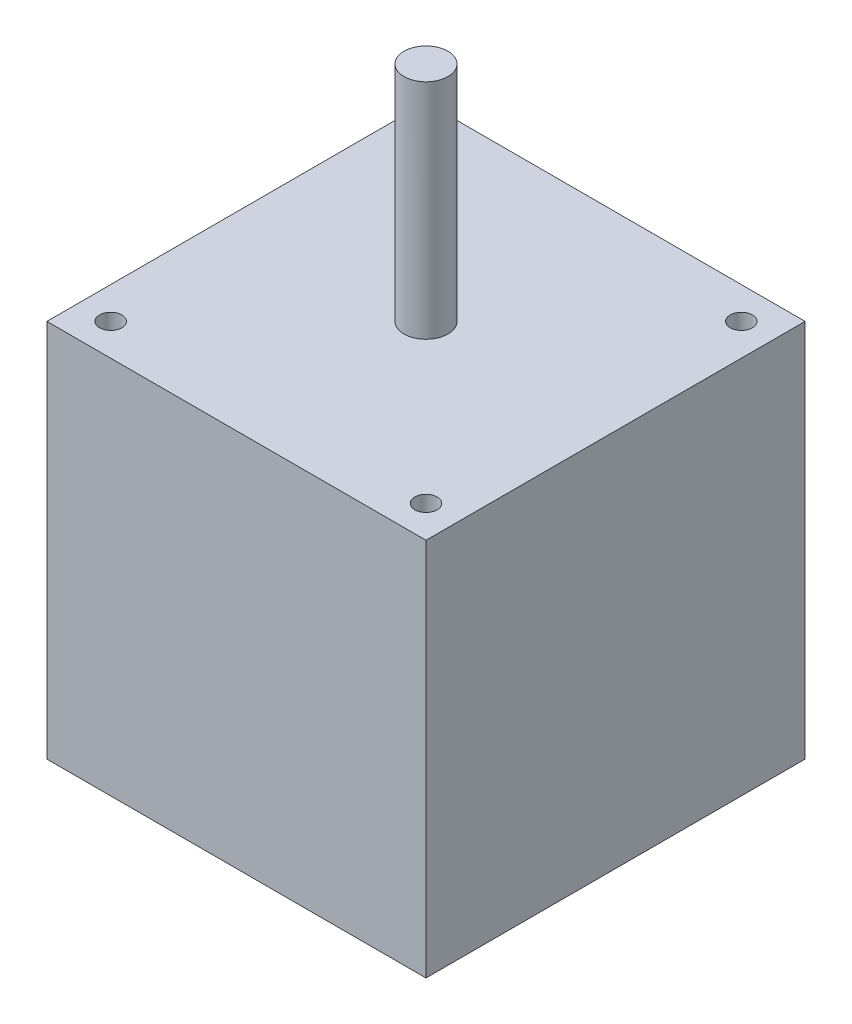
SolidWorks part; units mm, degrees
ref_plane "Front Plane" through (0, 0, 0) normal (0, 0, 1) x (1, 0, 0)
ref_plane "Top Plane" through (0, 0, 0) normal (0, 1, 0) x (1, 0, 0)
ref_plane "Right Plane" through (0, 0, 0) normal (1, 0, 0) x (0, 0, -1)
sketch "Sketch1" plane through (0, 0, 0) normal (0, 1, 0) x (1, 0, 0)
  line L1 (-21.59, -21.59) -> (21.59, -21.59)
  line L2 (-21.59, -21.59) -> (-21.59, 21.59)
  line L3 (-21.59, 21.59) -> (21.59, 21.59)
  line L4 (21.59, -21.59) -> (21.59, 21.59)
  line L5 (-21.59, -21.59) -> (21.59, 21.59) construction
  line L6 (-21.59, 21.59) -> (21.59, -21.59) construction
  point P0 (0, 0)
  dimension "D1" = 43.18
extrude "Boss-Extrude1" add sketch "Sketch1" along normal blind 43.18
sketch "Sketch2" plane through (0, 43.18, 0) normal (0, 1, 0) x (1, 0, 0)
  circle A0 centre (0, 0) radius 2.5
  dimension "D1" = 5
extrude "Boss-Extrude2" add sketch "Sketch2" along normal blind 25.4
sketch "Sketch3" plane through (0, 43.18, 0) normal (0, 1, 0) x (1, 0, 0)
  line L0 (0, 0) -> (-17.9605, 17.9605) construction
  line L2 (0, 0) -> (36.8461, 0) construction
  line L3 (0, 0) -> (0, 25.8104) construction
  circle A0 centre (-17.9605, 17.9605) radius 1.27
  dimension "D4" = 2.54
  dimension "D1" = 25.4
  dimension "D2" = 135
extrude "Cut-Extrude1" cut sketch "Sketch3" against normal up to surface (43.18 mm away) up to face at (0, 0, 0)
pattern_linear "LPattern1" count 2 spacing 35.9156 along (1, 0, 0) count 2 spacing 35.9156 along (0, 0, 1) of "Cut-Extrude1"
